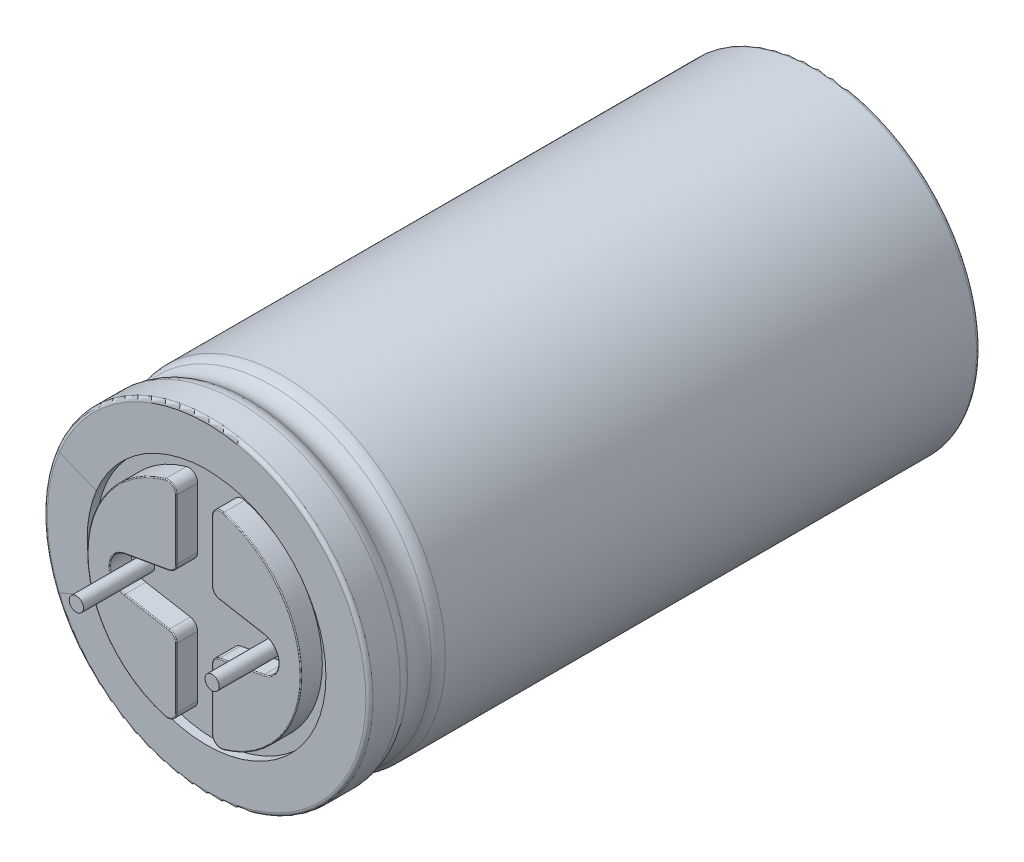
SolidWorks part; units mm, degrees
ref_plane "Płaszczyzna przednia" through (0, 0, 0) normal (0, 0, 1) x (1, 0, 0)
ref_plane "Płaszczyzna górna" through (0, 0, 0) normal (0, 1, 0) x (1, 0, 0)
ref_plane "Płaszczyzna prawa" through (0, 0, 0) normal (1, 0, 0) x (0, 0, -1)
sketch "Szkic1" plane through (0, 0, 0) normal (0, 1, 0) x (1, 0, 0)
  line L0 (0, 0.72) -> (0, 35)
  line L1 (0, 35) -> (8.94, 35)
  line L2 (9.14, 34.8) -> (9.14, 4.9837)
  line L3 (8.94, 0.72) -> (0, 0.72)
  line L4 (9.14, 2.4563) -> (9.14, 0.92)
  arc A0 (8.9463, 3.0479) -> (8.9463, 4.3921) centre (9.8623, 3.72) cw
  arc A1 (8.94, 35) -> (9.14, 34.8) centre (8.94, 34.8) cw
  arc A2 (9.14, 0.92) -> (8.94, 0.72) centre (8.94, 0.92) cw
  arc A3 (8.9463, 3.0479) -> (9.14, 2.4563) centre (8.14, 2.4563) cw
  arc A4 (8.9463, 4.3921) -> (9.14, 4.9837) centre (8.14, 4.9837) ccw
  point P7 (9.14, 35)
  dimension "D3" = 1
  dimension "D4" = 8.14
  dimension "D5" = 8.9463
  dimension "D1" = 1.1361
  dimension "D2" = 0.2
  dimension "D6" = 0.72
  dimension "D7" = 2.4563
  dimension "D12" = 35
revolve "Obrót1" add sketch "Szkic1" angle 360 about L0
sketch "Szkic2" plane through (0, 0, -35) normal (0, 0, -1) x (-1, 0, 0)
  circle A0 centre (0, 0) radius 6.7
  circle A1 centre (0, 0) radius 8.94 construction
  dimension "D1" = 13.4
extrude "Wytnij-wyciągnięcie1" cut sketch "Szkic2" against normal blind 0.2
sketch "Szkic3" plane through (0, 0, -34.8) normal (0, 0, -1) x (-1, 0, 0)
  line L0 (0, 0) -> (0, 6) construction
  line L1 (0.1, 0) -> (0.1, 6)
  line L2 (-0.1, 0) -> (-0.1, 6)
  arc A0 (0.1, 0) -> (-0.1, 0) centre (0, 0) cw
  arc A1 (0.1, 6) -> (-0.1, 6) centre (0, 6) ccw
  dimension "D1" = 6
  dimension "D2" = 0.1
extrude "Wytnij-wyciągnięcie2" cut sketch "Szkic3" against normal blind 0.2
pattern_circular "Szyk kołowy1" count 4 over 360 about axis through (0, 0, 0) along (0, 0, 1) of "Wytnij-wyciągnięcie2"
sketch "Szkic4" plane through (0, 0, -0.72) normal (0, 0, 1) x (1, 0, 0)
  circle A0 centre (0, 0) radius 6.7
  dimension "D1" = 13.4
extrude "Wytnij-wyciągnięcie3" cut sketch "Szkic4" against normal blind 0.5
sketch "Szkic5" plane through (0, 0, -1.22) normal (0, 0, 1) x (1, 0, 0)
  line L2 (1, -1.9189) -> (1, -5.2915)
  line L3 (1, 1.9189) -> (1, 5.2915)
  line L7 (1.4124, -1.4266) -> (3.9098, -0.9822)
  line L8 (1.4124, 1.4266) -> (3.9098, 0.9822)
  arc A0 (1.6364, -5.7725) -> (1.6364, 5.7725) centre (0, 0) ccw
  arc A1 (3.9098, -0.9822) -> (3.9098, 0.9822) centre (3.735, 0) ccw
  arc A2 (1.6364, -5.7725) -> (1, -5.2915) centre (1.5, -5.2915) cw
  arc A3 (1.4124, -1.4266) -> (1, -1.9189) centre (1.5, -1.9189) ccw
  arc A4 (1.6364, 5.7725) -> (1, 5.2915) centre (1.5, 5.2915) ccw
  arc A5 (1.4124, 1.4266) -> (1, 1.9189) centre (1.5, 1.9189) cw
  circle A6 centre (0, 0) radius 6.7 construction
  dimension "D3" = 2.4974
  dimension "D2" = 0.9977
  dimension "D1" = 6
  dimension "D4" = 1
  dimension "D5" = 1.4124
  dimension "D6" = 3.735
extrude "Dodanie-wyciągnięcie1" add sketch "Szkic5" along normal blind 1.2 separate body
fillet "Zaokrąglenie1" radius 0.05 10 edges at (1, -3.6052, -0.02) (1.1167, -1.5978, -0.02) (2.6611, -1.2044, -0.02) (4.7327, 0, -0.02) (2.6611, 1.2044, -0.02) (1.1167, 1.5978, -0.02) (1, 3.6052, -0.02) (1.1985, 5.6904, -0.02) (6, 0, -0.02) (1.1985, -5.6904, -0.02)
sketch "Szkic9" plane through (0, 0, 0) normal (1, 0, 0) x (0, 0, -1)
  line L0 (0.72, 0) -> (0.72, -3.5)
  line L1 (0.72, -3.5) -> (41.36, -3.5)
  line L2 (41.36, -3.5) -> (41.36, 3.5)
  line L3 (41.36, 3.5) -> (0.72, 3.5)
  line L4 (0.72, 3.5) -> (0.72, 0)
  line L6 (31.54, 0.7) -> (28.54, 0.7)
  line L7 (31.54, 1) -> (28.54, 1)
  line L8 (31.54, -1) -> (28.54, -1)
  line L9 (31.54, -0.7) -> (28.54, -0.7)
  line L20 (13.54, 0.7) -> (10.54, 0.7)
  line L21 (13.54, 1) -> (10.54, 1)
  line L22 (13.54, -1) -> (10.54, -1)
  line L23 (13.54, -0.7) -> (10.54, -0.7)
  arc A0 (31.54, 1) -> (31.54, -1) centre (31.54, 0) cw
  arc A1 (28.54, 1) -> (28.54, -1) centre (28.54, 0) ccw
  arc A2 (28.54, 0.7) -> (28.54, -0.7) centre (28.54, 0) ccw
  arc A3 (31.54, 0.7) -> (31.54, -0.7) centre (31.54, 0) cw
  arc A8 (13.54, 1) -> (13.54, -1) centre (13.54, 0) cw
  arc A9 (10.54, 1) -> (10.54, -1) centre (10.54, 0) ccw
  arc A10 (10.54, 0.7) -> (10.54, -0.7) centre (10.54, 0) ccw
  arc A11 (13.54, 0.7) -> (13.54, -0.7) centre (13.54, 0) cw
  dimension "D6" = 28.54
  dimension "D2" = 0.7
  dimension "D5" = 13.54
  dimension "D7" = 3.5
  dimension "D8" = 41.36
  dimension "D1" = 1
  dimension "D3" = 0.72
  dimension "D4" = 10.54
split line "Linia podziałowa1"
sketch "Szkic11" plane through (0, 0, -1.22) normal (0, 0, 1) x (1, 0, 0)
  line L0 (0, 0) -> (-3.81, 0) construction
  line L1 (0, 0) -> (3.81, 0) construction
  circle A0 centre (-3.81, 0) radius 0.4
  circle A1 centre (3.81, 0) radius 0.4
  dimension "D3" = 0.8
  dimension "D4" = 0.8
  dimension "D1" = 3.81
  dimension "D2" = 3.81
extrude "Dodanie-wyciągnięcie2" add sketch "Szkic11" along normal blind 4 separate body
sketch "Szkic12" plane through (0, 0, 0) normal (0, 0, 1) x (1, 0, 0)
  line L0 (0, 0) -> (-9.14, 0) construction
  line L4 (-6.1893, 2.5656) -> (-8.4433, 3.5)
  line L5 (-6.1893, -2.5656) -> (-8.4433, -3.5)
  arc A0 (-8.4433, 3.5) -> (-8.4433, -3.5) centre (0, 0) ccw
  arc A1 (-6.1893, 2.5656) -> (-6.1893, -2.5656) centre (0, 0) ccw
  dimension "D1" = 9.14
  dimension "D2" = 6.7
  dimension "D3" = 6.1893
split line "Linia podziałowa2"
pattern_circular "Szyk kołowy3" count 2 over 180 about axis through (0, 0, 0) along (0, 0, 1) of bodies 106
